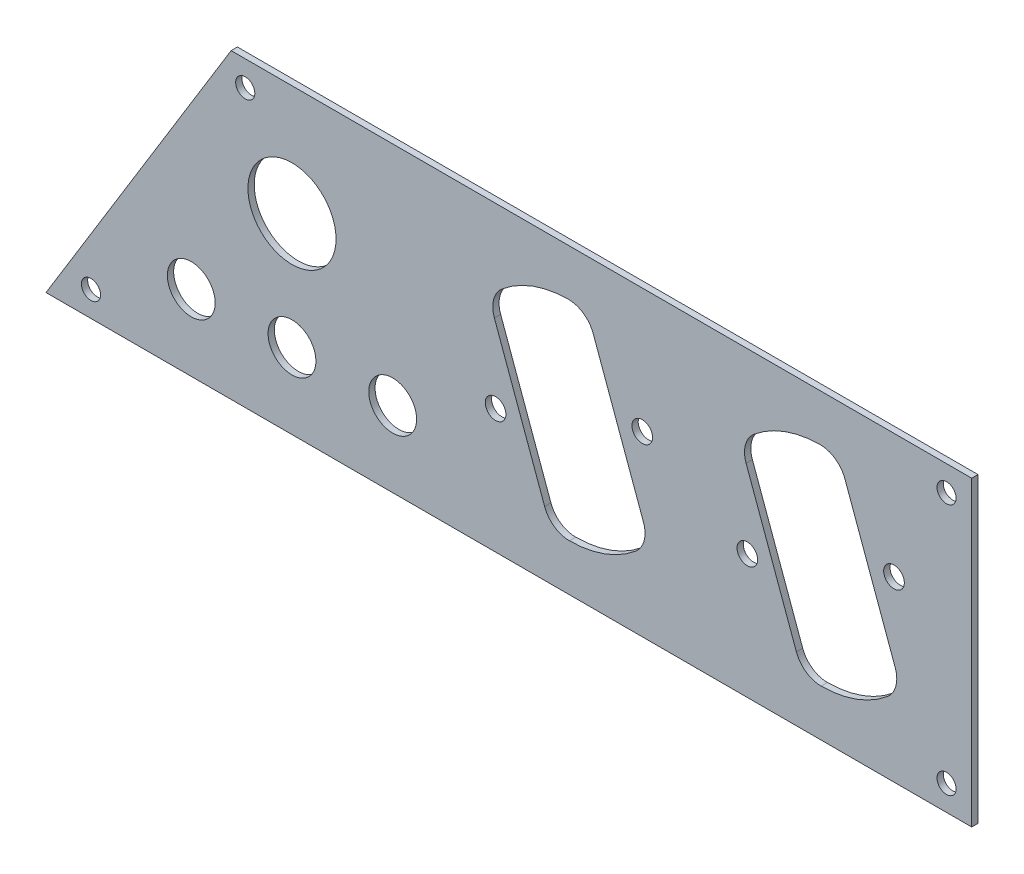
SolidWorks part; units mm, degrees
material "6061-T6 (SS)"
ref_plane "Front Plane" through (0, 0, 0) normal (0, 0, 1) x (1, 0, 0)
ref_plane "Top Plane" through (0, 0, 0) normal (0, 1, 0) x (1, 0, 0)
ref_plane "Right Plane" through (0, 0, 0) normal (1, 0, 0) x (0, 0, -1)
sketch "Sketch1" plane through (0, 0, 0) normal (0, 0, 1) x (1, 0, 0)
  line L0 (-233.4954, -381) -> (-186.7963, -304.8)
  line L1 (-186.7963, -304.8) -> (0, -304.8)
  line L2 (0, -304.8) -> (0, -381)
  line L3 (0, -381) -> (-233.4954, -381)
  line L4 (-186.7963, -304.8) -> (0, 0) construction
  line L5 (0, 0) -> (0, -304.8) construction
  line L8 (-196.85, -361.95) -> (-171.45, -361.95) construction
  line L9 (-171.45, -361.95) -> (-146.05, -361.95) construction
  line L19 (-183.2403, -311.15) -> (-222.1562, -374.65) construction
  circle A6 centre (-171.45, -332.74) radius 11.1125
  circle A9 centre (-196.85, -361.95) radius 6.0325
  circle A10 centre (-171.45, -361.95) radius 6.0325
  circle A11 centre (-146.05, -361.95) radius 6.0325
  circle A12 centre (-171.45, -332.74) radius 14.9225 construction
  circle A13 centre (-196.85, -361.95) radius 7.3025 construction
  circle A14 centre (-171.45, -361.95) radius 7.3025 construction
  circle A15 centre (-146.05, -361.95) radius 7.3025 construction
  circle A24 centre (-6.35, -311.15) radius 2.413
  circle A25 centre (-6.35, -374.65) radius 2.413
  circle A26 centre (-222.1562, -374.65) radius 2.413
  circle A27 centre (-183.2403, -311.15) radius 2.413
  point P32 (0, -342.9)
  line B0 (-56.5978, -349.6327) -> (-19.6022, -336.1673) construction
  line B1 (-44.1734, -352.206) -> (-37.9837, -369.212) construction
  line B2 (-21.276, -363.1309) -> (-27.4657, -346.1248) construction
  line B3 (-32.0266, -333.594) -> (-38.2163, -316.588) construction
  line B4 (-48.7343, -339.6752) -> (-54.924, -322.6691) construction
  line B5 (-54.924, -322.6691) -> (-38.2163, -316.588) construction
  line B6 (-37.9837, -369.212) -> (-21.276, -363.1309) construction
  line B7 (-28.4136, -369.513) -> (-47.7864, -316.287) construction
  line B8 (-56.9042, -330.003) -> (-44.2149, -364.8668)
  line B9 (-31.9851, -320.9332) -> (-19.2958, -355.797)
  circle B10 centre (-38.1, -342.9) radius 11.1125 construction
  circle B11 centre (-19.6022, -336.1673) radius 2.6035
  circle B12 centre (-56.5978, -349.6327) radius 2.6035
  circle B13 centre (-38.1, -342.9) radius 28.321 construction
  arc B14 (-37.9837, -369.212) -> (-21.276, -363.1309) centre (-38.0847, -342.942) ccw
  arc B15 (-27.4657, -346.1248) -> (-32.0266, -333.594) centre (-38.1, -342.9) ccw construction
  arc B16 (-44.1734, -352.206) -> (-48.7343, -339.6752) centre (-38.1, -342.9) cw construction
  arc B17 (-54.924, -322.6691) -> (-38.2163, -316.588) centre (-38.1153, -342.858) cw
  arc B18 (-54.924, -322.6691) -> (-56.9042, -330.003) centre (-50.6985, -327.7443) ccw
  arc B19 (-38.2163, -316.588) -> (-31.9851, -320.9332) centre (-38.1909, -323.1919) cw
  arc B20 (-21.276, -363.1309) -> (-19.2958, -355.797) centre (-25.5015, -358.0557) ccw
  arc B21 (-44.2149, -364.8668) -> (-37.9837, -369.212) centre (-38.0091, -362.6081) ccw
  line B22 (-120.4042, -330.003) -> (-107.7149, -364.8668)
  line B23 (-95.4851, -320.9332) -> (-82.7958, -355.797)
  circle B24 centre (-83.1022, -336.1673) radius 2.6035
  circle B25 centre (-120.0978, -349.6327) radius 2.6035
  arc B26 (-101.4837, -369.212) -> (-84.776, -363.1309) centre (-101.5847, -342.942) ccw
  arc B27 (-118.424, -322.6691) -> (-101.7163, -316.588) centre (-101.6153, -342.858) cw
  arc B28 (-118.424, -322.6691) -> (-120.4042, -330.003) centre (-114.1985, -327.7443) ccw
  arc B29 (-101.7163, -316.588) -> (-95.4851, -320.9332) centre (-101.6909, -323.1919) cw
  arc B30 (-84.776, -363.1309) -> (-82.7958, -355.797) centre (-89.0015, -358.0557) ccw
  arc B31 (-107.7149, -364.8668) -> (-101.4837, -369.212) centre (-101.5091, -362.6081) ccw
sketch_block_instance "Block1-1"
sketch_block "Block1" parameters "D1"=22.225, "D3"=5.207, "D4"=56.642, "D8"=6.604, "D2"=39.37, "D5"=17.78, "D6"=52.451, "D7"=49.53
sketch_block_instance "Block1-2" parameters "D4"=45.2595, "D7"=6.8204, "D9"=22.225, "D10"=19.12, "D11"=40.9447, "D12"=10.1765, "D13"=0, "D14"=15.5057, "D21"=6.2968, "D22"=8.89, "D23"=14.1662, "D24"=5.311, "D26"=6.1234, "D27"=6.35, "D1"=59.6383, "D2"=158.824, "D3"=112.0581, "D5"=43.181, "D6"=44.4211, "D8"=38.4622, "D15"=18.1242, "D16"=30.082, "D17"=26.5954, "D18"=188.7103, "D19"=33.3325, "D20"=59.926, "D25"=5.6827, "D28"=6.4898, "D29"=74.4762
extrude "Panel" add sketch "Sketch1" along normal blind 1.5875
fillet "Sharp Edge Fillet" [suppressed] radius 2.54
